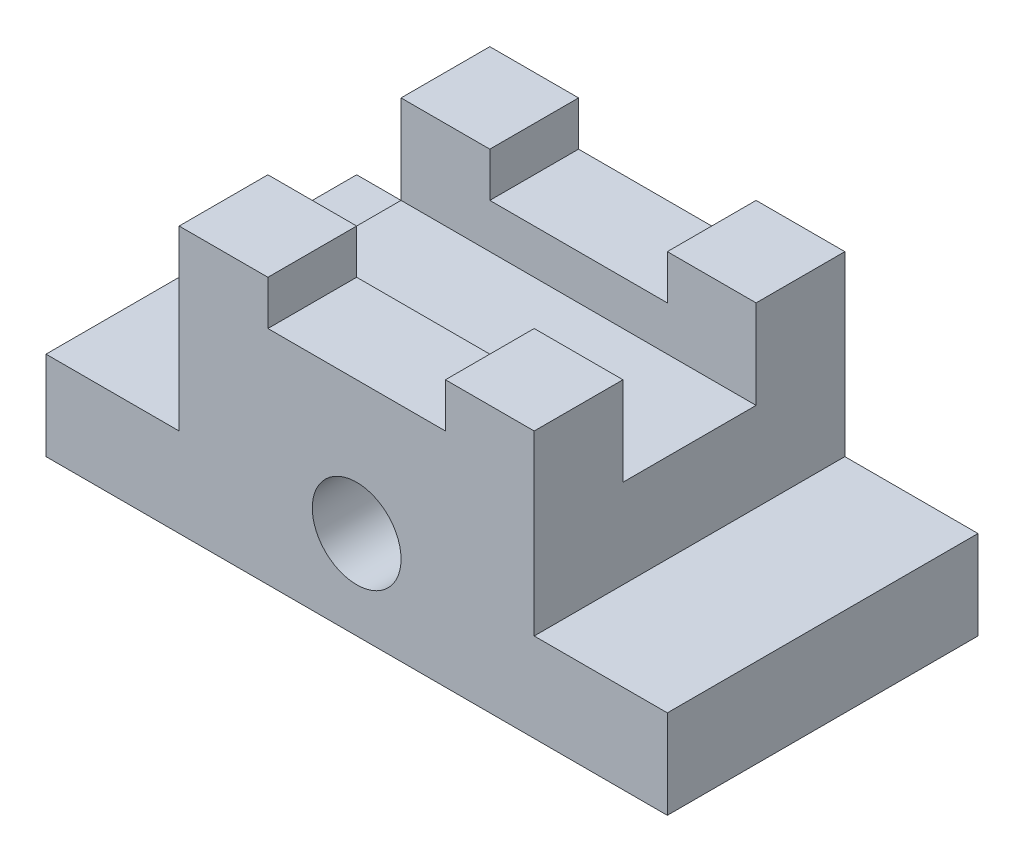
SolidWorks part; units mm, degrees
ref_plane "Front Plane" through (0, 0, 0) normal (0, 0, 1) x (1, 0, 0)
ref_plane "Top Plane" through (0, 0, 0) normal (0, 1, 0) x (1, 0, 0)
ref_plane "Right Plane" through (0, 0, 0) normal (1, 0, 0) x (0, 0, -1)
sketch "Sketch1" plane through (0, 0, 0) normal (0, 1, 0) x (1, 0, 0)
  line L1 (0, 0) -> (70, 0)
  line L2 (0, 0) -> (0, 35)
  line L3 (0, 35) -> (70, 35)
  line L4 (70, 0) -> (70, 35)
  dimension "D1" = 35
  dimension "D2" = 70
extrude "Boss-Extrude1" add sketch "Sketch1" along normal blind 30
sketch "Sketch2" plane through (0, 30, 0) normal (0, 1, 0) x (1, 0, 0)
  line L0 (70, 35) -> (0, 35) construction
  line L1 (0, 0) -> (15, 0)
  line L2 (0, 0) -> (0, 35)
  line L3 (0, 35) -> (15, 35)
  line L4 (15, 0) -> (15, 35)
  dimension "D1" = 15
extrude "Cut-Extrude1" cut sketch "Sketch2" against normal blind 20
sketch "Sketch3" plane through (0, 30, 0) normal (0, 1, 0) x (1, 0, 0)
  line L0 (15, 0) -> (70, 0) construction
  line L1 (70, 35) -> (55, 35)
  line L2 (70, 35) -> (70, 0)
  line L3 (70, 0) -> (55, 0)
  line L4 (55, 35) -> (55, 0)
  dimension "D1" = 15
extrude "Cut-Extrude2" cut sketch "Sketch3" against normal blind 20
sketch "Sketch4" plane through (55, 0, 0) normal (1, 0, 0) x (0, 0, -1)
  line L0 (35, 30) -> (25, 30) construction
  line L1 (35, 30) -> (0, 30) construction
  line L3 (25, 30) -> (10, 30)
  line L4 (25, 30) -> (25, 20)
  line L5 (25, 20) -> (10, 20)
  line L6 (10, 30) -> (10, 20)
  dimension "D1" = 10
  dimension "D2" = 15
  dimension "D3" = 10
extrude "Cut-Extrude3" cut sketch "Sketch4" against normal blind 41
sketch "Sketch5" plane through (0, 30, 0) normal (0, 1, 0) x (1, 0, 0)
  line L0 (15, 0) -> (25, 0) construction
  line L1 (15, 0) -> (55, 0) construction
  dimension "D1" = 10
sketch "Sketch6" plane through (0, 0, 0) normal (0, 0, 1) x (1, 0, 0)
  line L1 (25, 30) -> (45, 30)
  line L2 (25, 30) -> (25, 25)
  line L3 (25, 25) -> (45, 25)
  line L4 (45, 30) -> (45, 25)
  dimension "D1" = 20
  dimension "D2" = 5
extrude "Cut-Extrude4" cut sketch "Sketch6" against normal blind 41
sketch "Sketch7" plane through (0, 0, 0) normal (0, 0, 1) x (1, 0, 0)
  line L0 (0, 0) -> (35, 0) construction
  line L1 (0, 0) -> (70, 0) construction
  line L2 (35, 0) -> (35, 10) construction
  circle A0 centre (35, 10) radius 5
  dimension "D2" = 10
  dimension "D1" = 10
extrude "Cut-Extrude5" cut sketch "Sketch7" against normal through all
